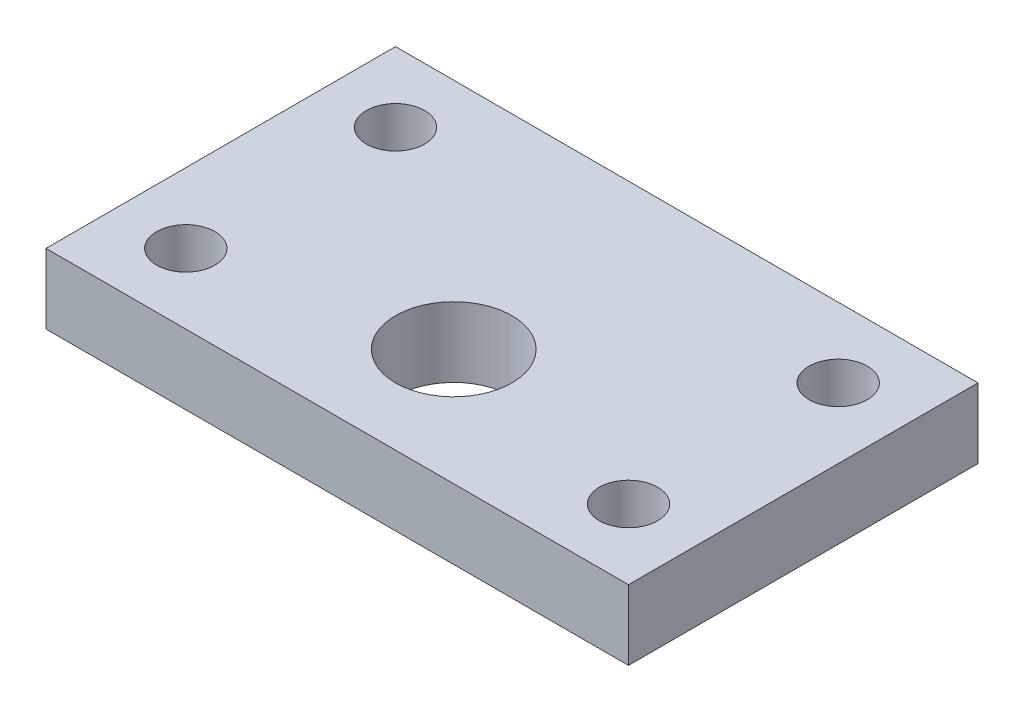
SolidWorks part; units mm, degrees
ref_plane "Front Plane" through (0, 0, 0) normal (0, 0, 1) x (1, 0, 0)
ref_plane "Top Plane" through (0, 0, 0) normal (0, 1, 0) x (1, 0, 0)
ref_plane "Right Plane" through (0, 0, 0) normal (1, 0, 0) x (0, 0, -1)
sketch "Sketch1" plane through (0, 0, 0) normal (0, 1, 0) x (1, 0, 0)
  line L1 (-125, -48) -> (125, -48)
  line L2 (-125, -48) -> (-125, 102)
  line L3 (-125, 102) -> (125, 102)
  line L4 (125, -48) -> (125, 102)
  circle A0 centre (-95, 72) radius 12.5
  circle A1 centre (95, 72) radius 12.5
  circle A2 centre (95, -18) radius 12.5
  circle A3 centre (-95, -18) radius 12.5
  circle A4 centre (0, 2) radius 25
  point P0 (0, 0)
  dimension "D3" = 2
  dimension "D1" = 150
  dimension "D2" = 250
  dimension "D5" = 125
  dimension "D6" = 50
  dimension "D4" = 2
extrude "Boss-Extrude1" add sketch "Sketch1" along normal mid plane 30
